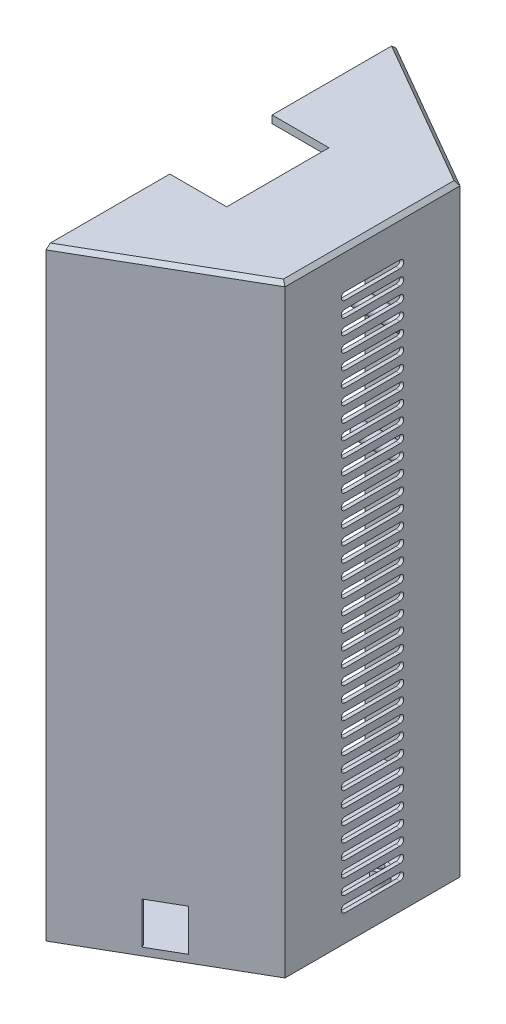
SolidWorks part; units mm, degrees
ref_plane "Front Plane" through (0, 0, 0) normal (0, 0, 1) x (1, 0, 0)
ref_plane "Top Plane" through (0, 0, 0) normal (0, 1, 0) x (1, 0, 0)
ref_plane "Right Plane" through (0, 0, 0) normal (1, 0, 0) x (0, 0, -1)
sketch "Sketch4" plane through (0, 0, 0) normal (0, 1, 0) x (1, 0, 0)
  line L0 (0, 46.188) -> (0, 45.0333)
  line L1 (0, -46.188) -> (40, -23.094)
  line L2 (40, -23.094) -> (40, 23.094)
  line L3 (40, 23.094) -> (0, 46.188)
  line L7 (0, -45.0333) -> (39, -22.5167)
  line L8 (39, -22.5167) -> (39, 22.5167)
  line L9 (39, 22.5167) -> (0, 45.0333)
  line L13 (0, -46.188) -> (0, -45.0333)
  line L15 (-40, -23.094) -> (0, -46.188) [skipped]
  line L16 (-39, -22.5167) -> (0, -45.0333) [skipped]
  line L17 (-39, 22.5167) -> (-39, -22.5167) [skipped]
  line L18 (-40, 23.094) -> (-40, -23.094) [skipped]
  line L19 (0, 45.0333) -> (-39, 22.5167) [skipped]
  line L20 (0, 46.188) -> (-40, 23.094) [skipped]
  dimension "D1" = 92.376
  dimension "D2" = 90.0666
extrude "Boss-Extrude5" add sketch "Sketch4" along normal blind 155
sketch "Sketch5" plane through (0, 0, 0) normal (0, -1, 0) x (1, 0, 0)
  line L0 (0, 46.188) -> (40, 23.094)
  line L1 (40, 23.094) -> (40, -23.094)
  line L2 (40, -23.094) -> (0, -46.188)
  line L3 (0, -46.188) -> (0, 46.188)
extrude "Boss-Extrude6" add sketch "Sketch5" along normal blind 2
sketch "Sketch6" plane through (0, 0, 0) normal (0, 1, 0) x (1, 0, 0)
  line L0 (0, -45.0333) -> (0, -38.0333)
  line L1 (0, -45.0333) -> (0, 45.0333) construction
  line L2 (0, 45.0333) -> (0, 38.0333)
  line L3 (0, -38.0333) -> (12.1244, -38.0333)
  line L4 (39, -22.5167) -> (0, -45.0333) construction
  line L5 (12.1244, -38.0333) -> (0, -45.0333)
  line L6 (0, 38.0333) -> (12.1244, 38.0333)
  line L7 (0, 45.0333) -> (39, 22.5167) construction
  line L8 (12.1244, 38.0333) -> (0, 45.0333)
  dimension "D1" = 7
  dimension "D2" = 7
extrude "Boss-Extrude7" add sketch "Sketch6" along normal blind 155
sketch "Sketch11" plane through (39, 0, 0) normal (-1, 0, 0) x (0, 0, 1)
  line L0 (-22.5167, 155) -> (22.5167, 155) construction
  line L1 (0, 147) -> (-7.25, 147)
  line L2 (0, 155) -> (0, 0) construction
  line L3 (-22.5167, 0) -> (22.5167, 0) construction
  line L4 (0, 147) -> (7.25, 147)
  line L5 (0, 145) -> (7.25, 145)
  line L6 (0, 145) -> (-7.25, 145)
  arc A0 (-7.25, 147) -> (-7.25, 145) centre (-7.25, 146) ccw
  arc A1 (7.25, 147) -> (7.25, 145) centre (7.25, 146) cw
  dimension "D1" = 7.25
  dimension "D2" = 7.25
  dimension "D3" = 7.25
  dimension "D4" = 7.25
  dimension "D5" = 2
  dimension "D6" = 8
extrude "Cut-Extrude1" cut sketch "Sketch11" against normal blind 2
pattern_linear "LPattern1" count 36 spacing 4 along (0, -1, 0) of "Cut-Extrude1"
sketch "Sketch12" plane through (0, 155, 0) normal (0, 1, 0) x (1, 0, 0)
  line L0 (0, 46.188) -> (40, 23.094)
  line L1 (40, 23.094) -> (40, -23.094)
  line L2 (40, -23.094) -> (0, -46.188)
  line L3 (0, -46.188) -> (0, 46.188)
extrude "Boss-Extrude10" add sketch "Sketch12" along normal blind 2
chamfer "Chamfer2" distance 1 angle 45 3 edges at (20, 157, -34.641) (40, 157, 0) (20, 157, 34.641)
sketch "Sketch13" plane through (0, 157, 0) normal (0, 1, 0) x (1, 0, 0)
  line L1 (-15, 13.5) -> (15, 13.5)
  line L2 (-15, 13.5) -> (-15, -13.5)
  line L3 (-15, -13.5) -> (15, -13.5)
  line L4 (15, 13.5) -> (15, -13.5)
  line L5 (-15, 13.5) -> (15, -13.5) construction
  line L6 (-15, -13.5) -> (15, 13.5) construction
  point P0 (0, 0)
  dimension "D1" = 30
  dimension "D2" = 27
extrude "Cut-Extrude2" cut sketch "Sketch13" against normal blind 10
sketch "Sketch15" plane through (39, 0, 0) normal (-1, 0, 0) x (0, 0, 1)
  line L0 (0, 155) -> (0, 0) construction
  line L1 (-22.5167, 155) -> (22.5167, 155) construction
  circle A0 centre (-10, 130) radius 2
  circle A1 centre (10, 130) radius 2
  circle A2 centre (-10, 130) radius 0.9
  circle A3 centre (10, 130) radius 0.9
  circle A4 centre (-10, 100) radius 2
  circle A5 centre (10, 100) radius 2
  circle A6 centre (10, 100) radius 0.9
  circle A7 centre (-10, 100) radius 0.9
  dimension "D1" = 4
  dimension "D2" = 4
  dimension "D3" = 10
  dimension "D4" = 10
  dimension "D5" = 25
  dimension "D6" = 25
  dimension "D7" = 1.8
  dimension "D8" = 1.8
  dimension "D9" = 4
  dimension "D10" = 4
  dimension "D11" = 30
  dimension "D12" = 30
  dimension "D13" = 10
  dimension "D15" = 1.8
  dimension "D16" = 1.8
  dimension "D14" = 10
extrude "Boss-Extrude11" add sketch "Sketch15" along normal blind 13
sketch "Sketch16" plane through (0, 0, 0) normal (0, 1, 0) x (1, 0, 0)
  line L0 (39, 22.5167) -> (39, -22.5167) construction
  line L2 (0, 38.0333) -> (12.1244, 38.0333) construction
  circle A0 centre (34, 8.0333) radius 2
  circle A1 centre (14, 8.0333) radius 2
  circle A2 centre (14, 8.0333) radius 0.9
  circle A3 centre (34, 8.0333) radius 0.9
  dimension "D1" = 4
  dimension "D2" = 4
  dimension "D4" = 20
  dimension "D5" = 30
  dimension "D6" = 30
  dimension "D7" = 1.8
  dimension "D8" = 1.8
  dimension "D3" = 5
extrude "Boss-Extrude12" add sketch "Sketch16" along normal blind 5
sketch "Sketch17" plane through (0, 0, 0) normal (-1, 0, 0) x (0, 0, 1)
  line L0 (-45.0333, 157) -> (-13.5, 157) construction
  line L2 (46.188, -2) -> (-46.188, -2) construction
  line L4 (13.5, 157) -> (45.0333, 157) construction
  line L6 (-46.188, 156) -> (-46.188, -2) construction
  line L7 (46.188, 156) -> (46.188, -2) construction
  circle A0 centre (-41.188, 132) radius 1.3
  circle A1 centre (-41.188, 78) radius 1.3
  circle A2 centre (-41.188, 23) radius 1.3
  circle A3 centre (41.188, 132) radius 1.3
  circle A4 centre (41.188, 78) radius 1.3
  circle A5 centre (41.188, 23) radius 1.3
  dimension "D1" = 2.6
  dimension "D2" = 2.6
  dimension "D3" = 2.6
  dimension "D5" = 25
  dimension "D6" = 79
  dimension "D7" = 2.6
  dimension "D8" = 2.6
  dimension "D9" = 2.6
  dimension "D13" = 5
  dimension "D14" = 5
  dimension "D16" = 5
  dimension "D17" = 5
  dimension "D18" = 5
  dimension "D4" = 25
  dimension "D10" = 25
  dimension "D11" = 79
  dimension "D12" = 25
  dimension "D15" = 5
extrude "Cut-Extrude3" cut sketch "Sketch17" against normal blind 5
sketch "Sketch18" plane through (19.5, 0, 33.775) normal (-0.5, 0, -0.866) x (-0.866, 0, 0.5)
  line L0 (-22.5167, 0) -> (8.5167, 0) construction
  line L1 (-4.4833, 11) -> (4.5167, 11)
  line L2 (-4.4833, 11) -> (-4.4833, 0)
  line L3 (-4.4833, 0) -> (4.5167, 0)
  line L4 (4.5167, 11) -> (4.5167, 0)
  line L5 (-4.4833, 11) -> (4.5167, 0) construction
  line L6 (-4.4833, 0) -> (4.5167, 11) construction
  line L7 (8.5167, 155) -> (8.5167, 0) construction
  point P0 (0.0167, 5.5)
  dimension "D1" = 11
  dimension "D2" = 9
  dimension "D3" = 0
  dimension "D4" = 4
extrude "Cut-Extrude4" cut sketch "Sketch18" against normal blind 10
